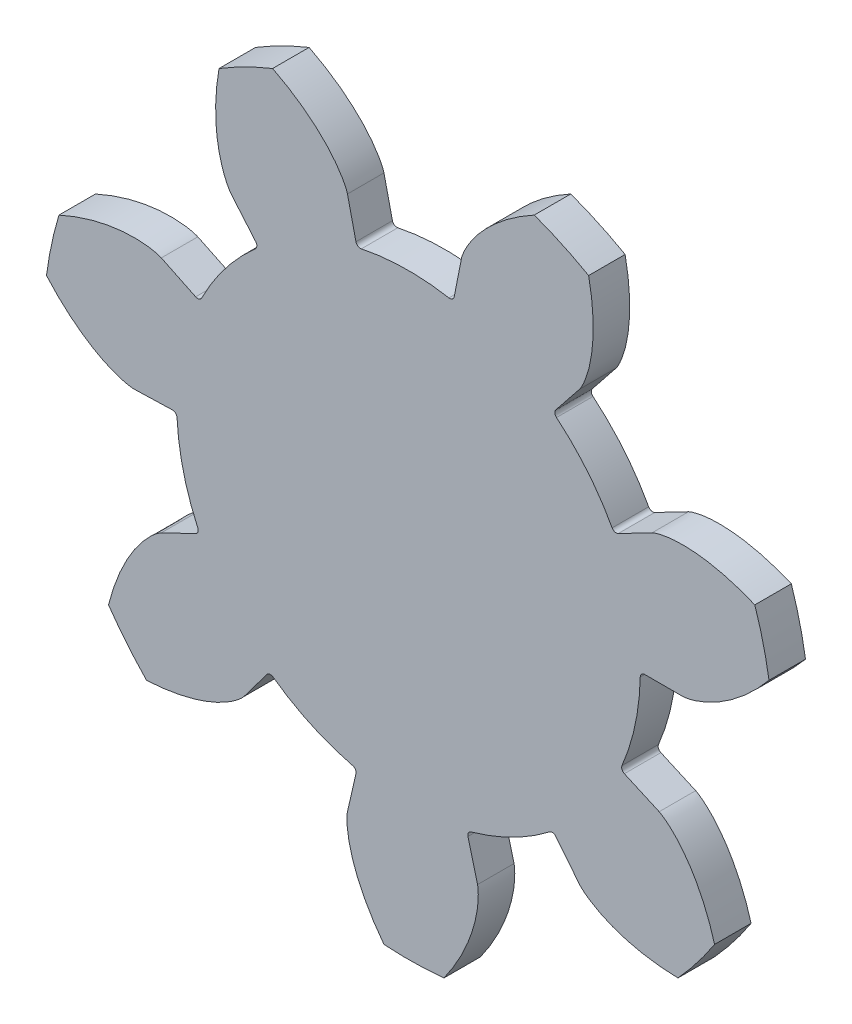
SolidWorks part; units mm, degrees
ref_plane "Front Plane" through (0, 0, 0) normal (0, 0, 1) x (1, 0, 0)
ref_plane "Top Plane" through (0, 0, 0) normal (0, 1, 0) x (1, 0, 0)
ref_plane "Right Plane" through (0, 0, 0) normal (1, 0, 0) x (0, 0, -1)
sketch "Sketch1" plane through (0, 0, 0) normal (0, 0, 1) x (1, 0, 0)
  circle A0 centre (0, 0) radius 254
  dimension "D1" = 508
extrude "Boss-Extrude1" add sketch "Sketch1" against normal blind 25.4
sketch "Sketch2" plane through (0, 0, 0) normal (0, 0, 1) x (1, 0, 0)
  line L0 (161.29, 0) -> (190.9455, 0)
  line L1 (0, 0) -> (248.4466, -52.8234) construction
  line L2 (147.3385, -65.6189) -> (174.4288, -77.6839)
  circle A0 centre (0, 0) radius 203.2 construction
  circle A1 centre (0, 0) radius 190.9455 construction
  arc A2 (147.3385, -65.6189) -> (161.29, 0) centre (0, 0) ccw
  circle A3 centre (0, 0) radius 254 construction
  spline S0 degree 4 poles (190.9455, 0) (191.0161, 0.0011) (191.1572, 0.0054) (191.5527, 0.0282) (192.2986, 0.0992) (193.4414, 0.2565) (194.9772, 0.5422) (196.9479, 0.9993) (199.247, 1.6469) (201.7464, 2.4738) (204.4308, 3.4943) (207.0758, 4.6203) (209.6787, 5.8401) (212.2399, 7.1451) (215.2972, 8.8237) (218.9067, 10.985) (223.019, 13.6976) (227.5756, 17.0298) (232.056, 20.6334) (236.3773, 24.4264) (240.0203, 27.8955) (243.0457, 30.968) (245.5018, 33.5891) (247.4293, 35.723) (249.3163, 37.8875) (251.169, 40.0906) (252.9774, 42.3149) (254.7589, 44.5862) (256.4849, 46.8583) (258.2038, 49.2052) (259.8338, 51.4983) (261.3115, 53.6576) (262.4212, 55.3151) (263.5051, 56.979) (264.0661, 57.8518) (264.8349, 59.0635) (265.4212, 60.0041) (266.0726, 61.0597) (266.6771, 62.0556) (267.3007, 63.0949) (267.9005, 64.1103) (268.3573, 64.8926) (268.6523, 65.4038) (268.8025, 65.6646) knots 0 0 0 0 0 0.002688 0.005377 0.015084 0.028532 0.04661 0.064855 0.092111 0.119476 0.146842 0.174209 0.201575 0.228941 0.256307 0.307035 0.361767 0.4165 0.471232 0.525964 0.580697 0.608063 0.635429 0.662795 0.690161 0.717528 0.744894 0.77226 0.799626 0.826992 0.854358 0.881725 0.895408 0.909091 0.920455 0.931818 0.943182 0.954545 0.965909 0.977273 0.988636 1 1 1 1 1 construction
  spline S1 degree 4 poles (190.9455, 0) (191.0161, 0.0011) (191.1572, 0.0054) (191.5527, 0.0282) (192.2986, 0.0992) (193.4414, 0.2565) (194.9772, 0.5422) (196.9479, 0.9993) (199.247, 1.6469) (201.7464, 2.4738) (204.4308, 3.4943) (207.0758, 4.6203) (209.6787, 5.8401) (212.2399, 7.1451) (215.2972, 8.8237) (218.9067, 10.985) (223.019, 13.6976) (227.5756, 17.0298) (232.056, 20.6334) (236.3773, 24.4264) (240.0203, 27.8955) (243.0457, 30.968) (245.5018, 33.5891) (247.4293, 35.723) (249.3163, 37.8875) (251.169, 40.0906) (252.9774, 42.3149) (254.7589, 44.5862) (256.4849, 46.8583) (258.2038, 49.2052) (259.8338, 51.4983) (261.3115, 53.6576) (262.4212, 55.3151) (263.3187, 56.693) (263.667, 57.232) (263.8434, 57.5068) knots 0 0 0 0 0 0.002688 0.005377 0.015084 0.028532 0.04661 0.064855 0.092111 0.119476 0.146842 0.174209 0.201575 0.228941 0.256307 0.307035 0.361767 0.4165 0.471232 0.525964 0.580697 0.608063 0.635429 0.662795 0.690161 0.717528 0.744894 0.77226 0.799626 0.826992 0.854358 0.881725 0.895408 0.909091 0.909091 0.909091 0.909091 0.909091
  spline S2 degree 4 poles (174.4288, -77.6839) (174.4928, -77.7137) (174.62, -77.775) (174.9719, -77.9567) (175.6244, -78.325) (176.6044, -78.9337) (177.8912, -79.8195) (179.5054, -81.0388) (181.3422, -82.5657) (183.2889, -84.3379) (185.326, -86.3623) (187.284, -88.467) (189.1656, -90.6402) (190.9743, -92.8743) (193.0842, -95.6516) (195.5022, -99.0944) (198.1552, -103.2454) (200.962, -108.1432) (203.5888, -113.2579) (205.9932, -118.4807) (207.9097, -123.1321) (209.4233, -127.1694) (210.6007, -130.5635) (211.4931, -133.2959) (212.3366, -136.0428) (213.1323, -138.8059) (213.8801, -141.5789) (214.5821, -144.3695) (215.2367, -147.162) (215.772, -149.6295) (216.1992, -151.7261) (216.5426, -153.5154) (216.7958, -154.88) (217.0594, -156.3863) (217.2739, -157.6445) (217.5318, -159.2614) (217.688, -160.2788) (217.9448, -162.0216) (218.1282, -163.3634) (218.3337, -164.9301) (218.5057, -166.3578) (218.6307, -167.4295) (218.7252, -168.2949) (218.7906, -168.9031) (218.8206, -169.1936) (218.8361, -169.3429) knots 0 0 0 0 0 0.002688 0.005377 0.015084 0.028532 0.04661 0.064855 0.092111 0.119476 0.146842 0.174209 0.201575 0.228941 0.256307 0.307035 0.361767 0.4165 0.471232 0.525964 0.580697 0.608063 0.635429 0.662795 0.690161 0.717528 0.744894 0.77226 0.799626 0.826992 0.840675 0.854358 0.868042 0.881725 0.895408 0.909091 0.920455 0.931818 0.954545 0.965909 0.977273 0.988636 0.994318 1 1 1 1 1 construction
  spline S3 degree 4 poles (174.4288, -77.6839) (174.4928, -77.7137) (174.62, -77.775) (174.9719, -77.9567) (175.6244, -78.325) (176.6044, -78.9337) (177.8912, -79.8195) (179.5054, -81.0388) (181.3422, -82.5657) (183.2889, -84.3379) (185.326, -86.3623) (187.284, -88.467) (189.1656, -90.6402) (190.9743, -92.8743) (193.0842, -95.6516) (195.5022, -99.0944) (198.1552, -103.2454) (200.962, -108.1432) (203.5888, -113.2579) (205.9932, -118.4807) (207.9097, -123.1321) (209.4233, -127.1694) (210.6007, -130.5635) (211.4931, -133.2959) (212.3366, -136.0428) (213.1323, -138.8059) (213.8801, -141.5789) (214.5821, -144.3695) (215.2367, -147.162) (215.772, -149.6295) (216.1992, -151.7261) (216.5426, -153.5154) (216.7958, -154.88) (217.0594, -156.3863) (217.2739, -157.6445) (217.4759, -158.9108) (217.5757, -159.5512) (217.6251, -159.8741) knots 0 0 0 0 0 0.002688 0.005377 0.015084 0.028532 0.04661 0.064855 0.092111 0.119476 0.146842 0.174209 0.201575 0.228941 0.256307 0.307035 0.361767 0.4165 0.471232 0.525964 0.580697 0.608063 0.635429 0.662795 0.690161 0.717528 0.744894 0.77226 0.799626 0.826992 0.840675 0.854358 0.868042 0.881725 0.895408 0.909091 0.909091 0.909091 0.909091 0.909091
  dimension "D1" = 406.4
  dimension "D2" = 381.8911
  dimension "D3" = 322.58
  dimension "D4" = 12.003
  dimension "D5" = 12.003
extrude "Cut-Extrude1" cut sketch "Sketch2" against normal through all and the other way through all
fillet "Fillet1" radius 3.175 2 edges at (161.29, 0, -12.7) (147.3385, -65.6189, -12.7)
pattern_circular "CirPattern1" count 7 over 360 about axis through (0, 0, -25.4) along (0, 0, 1) of "Cut-Extrude1", "Fillet1"
equation "\"P\"= 0.4375'Diameral Pitch"
equation "\"N\"= 7'Number of Teeth"
equation "\"phi\"= 20deg'Pressure Angle"
equation "\"a\"= .875 / \"P\"'Addendum"
equation "\"b\"= 1.25 / \"P\"'Dedendum"
equation "\"c\"= \"b\" - \"a\"'Clearence"
equation "\"dp\"= \"N\" / \"P\"'Pitch Circle Diameter"
equation "\"db\"= \"dp\" * cos ( \"phi\" )'Base Circle Diameter"
equation "\"D1@Sketch1\"= \"dp\" + 2 * \"a\"'Addendum Circle Diameter"
equation "\"D1@Sketch2\"= \"dp\"'Pitch Circle Diameter"
equation "\"D2@Sketch2\"= \"db\"'Base Circle Diameter"
equation "\"D3@Sketch2\"=12.7"
equation "\"alpha\"= sqr ( \"dp\" ^ 2 - \"db\" ^ 2 ) / \"db\" * 180 / pi - \"phi\""
equation "\"D4@Sketch2\"= 360 / ( 4 * \"N\" ) - \"alpha\""
equation "\"D5@Sketch2\"= 360 / ( 4 * \"N\" ) - \"alpha\""
